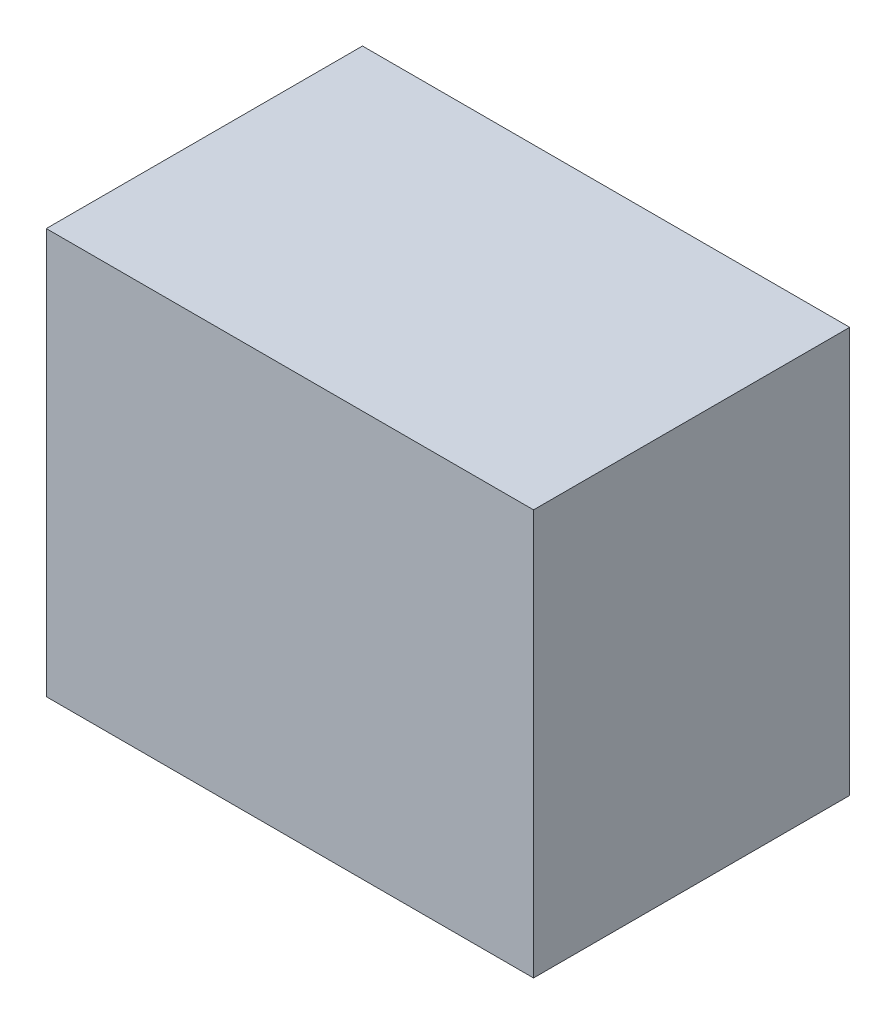
SolidWorks part; units mm, degrees
ref_plane "Front Plane" through (0, 0, 0) normal (0, 0, 1) x (1, 0, 0)
ref_plane "Top Plane" through (0, 0, 0) normal (0, 1, 0) x (1, 0, 0)
ref_plane "Right Plane" through (0, 0, 0) normal (1, 0, 0) x (0, 0, -1)
sketch "Sketch2" plane through (0, 0, 0) normal (0, 0, 1) x (1, 0, 0)
  line L1 (32.4422, -23.9751) -> (-15.3298, -23.9751)
  line L2 (32.4422, -23.9751) -> (32.4422, 15.7755)
  line L3 (32.4422, 15.7755) -> (-15.3298, 15.7755)
  line L4 (-15.3298, -23.9751) -> (-15.3298, 15.7755)
extrude "Boss-Extrude1" add sketch "Sketch2" along normal blind 31
